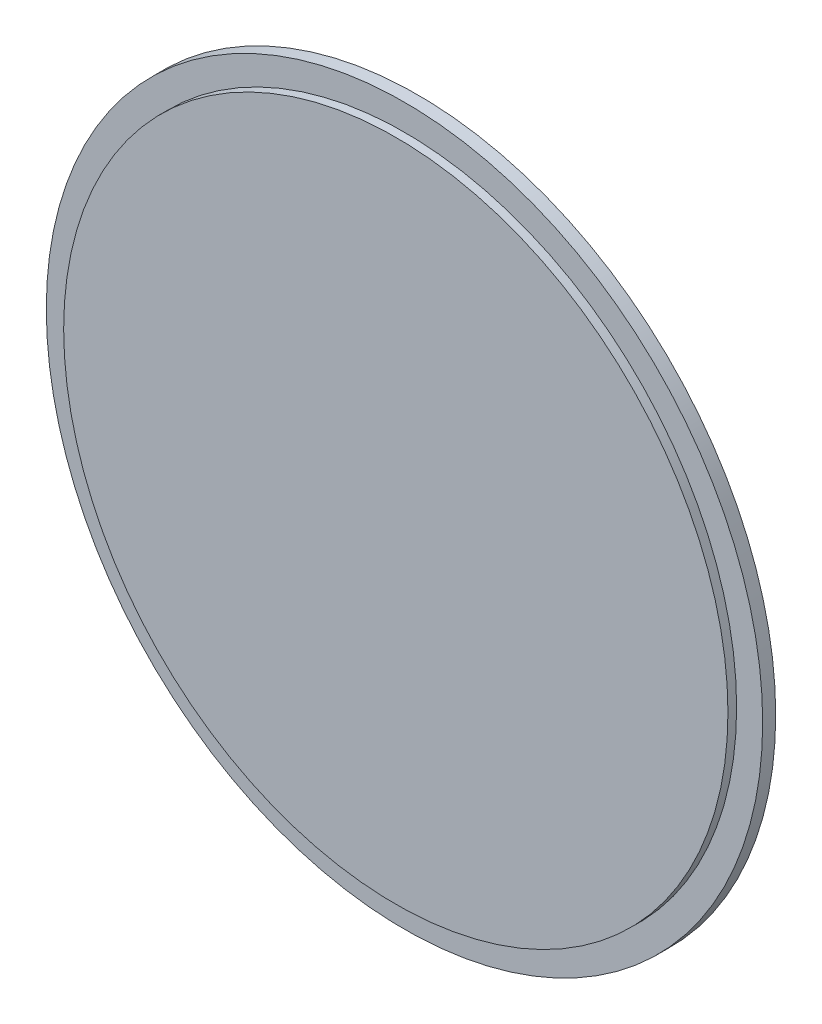
SolidWorks part; units mm, degrees
ref_plane "Plano frontal" through (0, 0, 0) normal (0, 0, 1) x (1, 0, 0)
ref_plane "Plano superior" through (0, 0, 0) normal (0, 1, 0) x (1, 0, 0)
ref_plane "Plano direito" through (0, 0, 0) normal (1, 0, 0) x (0, 0, -1)
sketch "Esboço1" plane through (0, 0, 0) normal (0, 0, 1) x (1, 0, 0)
  circle A0 centre (0, 0) radius 14 construction
  circle A1 centre (0, 0) radius 14
  circle A2 centre (0, 0) radius 82.5
  dimension "D1" = 165
extrude "Ressalto-extrusão1" add sketch "Esboço1" along normal blind 3
sketch "Esboço2" plane through (0, 0, 0) normal (0, 0, -1) x (-1, 0, 0)
  line L0 (0, 0) -> (15.1208, -54.9578)
  line L1 (0, 0) -> (40.0345, 40.5739)
  circle A1 centre (0, 0) radius 57 construction
  circle A2 centre (15.1208, -54.9578) radius 14 construction
  circle A3 centre (-55.1553, 14.3839) radius 14 construction
  circle A4 centre (40.0345, 40.5739) radius 14 construction
  circle A5 centre (-55.1553, 14.3839) radius 5.925
  circle A6 centre (40.0345, 40.5739) radius 5.925
  circle A7 centre (15.1208, -54.9578) radius 5.925
  point P14 (0, 0)
  dimension "D1" = 57
  dimension "D3" = 3
  dimension "D4" = 11.85
  dimension "D2" = 57
extrude "Ressalto-extrusão2" add sketch "Esboço2" along normal blind 8
sketch "Esboço3" plane through (0, 0, 3) normal (0, 0, 1) x (1, 0, 0)
  circle A0 centre (0, 0) radius 14
extrude "Ressalto-extrusão3" add sketch "Esboço3" against normal blind 3
sketch "Esboço4" plane through (0, 0, 3) normal (0, 0, 1) x (1, 0, 0)
  circle A0 centre (0, 0) radius 10
  circle A1 centre (0, 0) radius 14
  circle A2 centre (0, 0) radius 14 construction
  dimension "D1" = 0
extrude "Ressalto-extrusão4" add sketch "Esboço4" against normal up to surface (11 mm away) up to face at (49.2303, 14.3839, -8)
sketch "Esboço5" plane through (0, 0, -8) normal (0, 0, -1) x (-1, 0, 0)
  circle A0 centre (0, 0) radius 3.05
extrude "Corte-extrusão1" cut sketch "Esboço5" against normal blind 1
sketch "Esboço6" plane through (0, 0, 3) normal (0, 0, 1) x (1, 0, 0)
  circle A0 centre (0, 0) radius 77.5 construction
  circle A1 centre (0, 0) radius 76.5
  dimension "D1" = 1
extrude "Ressalto-extrusão5" add sketch "Esboço6" along normal blind 2
